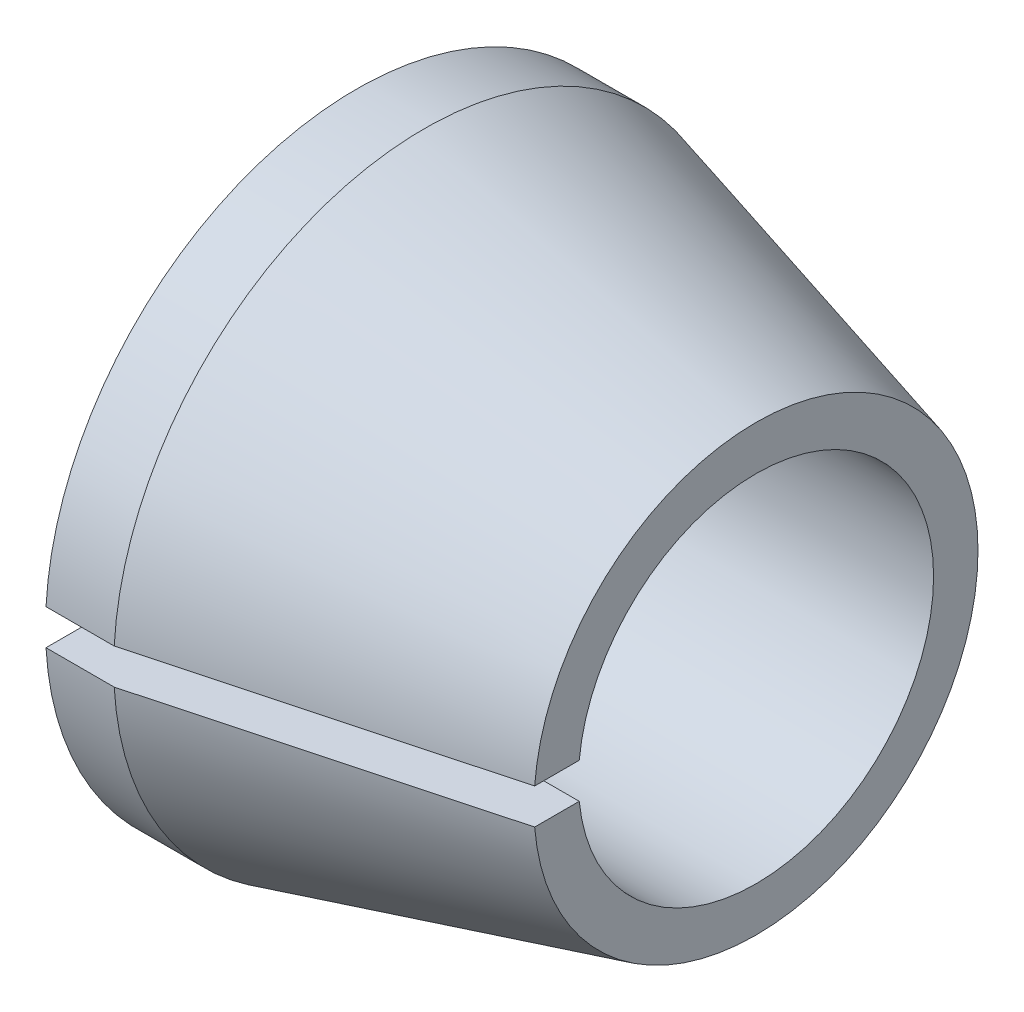
SolidWorks part; units mm, degrees
ref_plane "Ebene vorne" through (0, 0, 0) normal (0, 0, 1) x (1, 0, 0)
ref_plane "Ebene oben" through (0, 0, 0) normal (0, 1, 0) x (1, 0, 0)
ref_plane "Ebene rechts" through (0, 0, 0) normal (1, 0, 0) x (0, 0, -1)
sketch "Skizze1" plane through (0, 0, 0) normal (0, 0, 1) x (1, 0, 0)
  line L0 (0, 0) -> (11.5695, 0) construction
  line L1 (0, 4) -> (9, 4)
  line L2 (9, 5) -> (1.5359, 7)
  line L3 (1.5359, 7) -> (0, 7)
  line L4 (0, 7) -> (0, 4)
  line L5 (9, 4) -> (9, 5)
  dimension "D1" = 14
  dimension "D2" = 8
  dimension "D3" = 9
  dimension "D4" = 10
  dimension "D5" = 15
revolve "Rotation1" add sketch "Skizze1" angle 360 about L0
sketch "Skizze2" plane through (0, 0, 0) normal (1, 0, 0) x (0, 0, -1)
  line L1 (-10.0201, -0.4) -> (-3.9799, -0.4)
  line L2 (-10.0201, -0.4) -> (-10.0201, 0.4)
  line L3 (-10.0201, 0.4) -> (-3.9799, 0.4)
  line L4 (-3.9799, -0.4) -> (-3.9799, 0.4)
  line L5 (-10.0201, -0.4) -> (-3.9799, 0.4) construction
  line L6 (-10.0201, 0.4) -> (-3.9799, -0.4) construction
  circle A0 centre (0, 0) radius 7 construction
  circle A1 centre (0, 0) radius 4 construction
  circle A2 centre (0, 0) radius 7 construction
  point P0 (-7, 0)
  dimension "D1" = 0.8
extrude "Schnitt-Linear austragen1" cut sketch "Skizze2" along normal up to next
